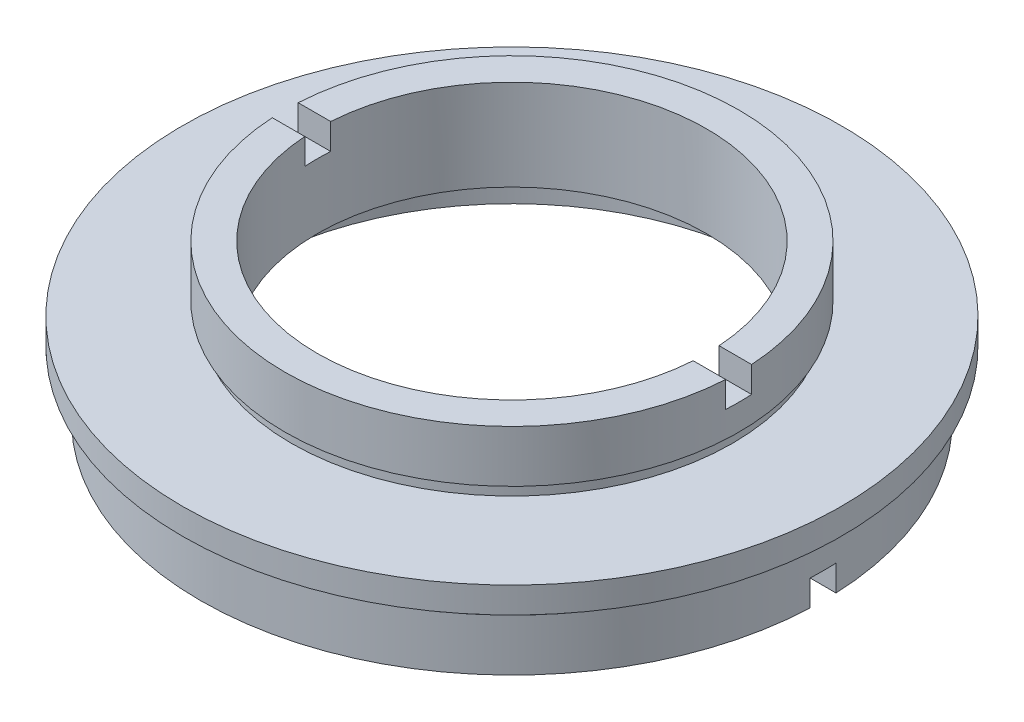
SolidWorks part; units mm, degrees
ref_plane "前视基准面" through (0, 0, 0) normal (0, 0, 1) x (1, 0, 0)
ref_plane "上视基准面" through (0, 0, 0) normal (0, 1, 0) x (1, 0, 0)
ref_plane "右视基准面" through (0, 0, 0) normal (1, 0, 0) x (0, 0, -1)
sketch "草图1" plane through (0, 0, 0) normal (0, 0, 1) x (1, 0, 0)
  line L0 (0, 22.6775) -> (0, 0) construction
  line L1 (-15, 12) -> (-17.5, 12)
  line L2 (-17.5, 12) -> (-17.5, 8)
  line L3 (-17.5, 8) -> (-17, 8)
  line L4 (-17, 8) -> (-17, 7)
  line L5 (-17, 7) -> (-25.4, 7)
  line L6 (-25.4, 7) -> (-25.4, 5)
  line L7 (-25.4, 5) -> (-23.5, 5)
  line L8 (-23.5, 5) -> (-23.5, 4)
  line L9 (-23.5, 4) -> (-24, 4)
  line L10 (-24, 4) -> (-24, 0)
  line L11 (-24, 0) -> (-20.5, 0)
  line L12 (-20.5, 0) -> (-20.5, 4)
  line L13 (-15, 5) -> (-21.1, 5)
  line L14 (-21.1, 5) -> (-21.1, 4)
  line L15 (-21.1, 4) -> (-20.5, 4)
  line L16 (-15, 12) -> (-15, 5)
  point P3 (-20.8, 4)
  point P5 (-25.4, 6)
  dimension "D2" = 1
  dimension "D3" = 1
  dimension "D4" = 5
  dimension "D5" = 5
  dimension "D6" = 17.5
  dimension "D7" = 25.4
  dimension "D8" = 24
  dimension "D9" = 23.5
  dimension "D10" = 17
  dimension "D11" = 20.5
  dimension "D12" = 0
  dimension "D13" = 21.1
  dimension "D14" = 15
  dimension "D15" = 12
  dimension "D16" = 7
  dimension "D17" = 1
revolve "旋转1" add sketch "草图1" angle 360 about L0
cosmetic thread "装饰螺纹线1"
cosmetic thread "装饰螺纹线2"
cosmetic thread "装饰螺纹线3"
cosmetic thread "装饰螺纹线4"
sketch "草图2" plane through (0, 0, 0) normal (1, 0, 0) x (0, 0, -1)
  line L0 (20.5, 12) -> (-20.5, 12) construction
  line L1 (-1, 13.594) -> (1, 13.594)
  line L2 (-1, 13.594) -> (-1, 10)
  line L3 (-1, 10) -> (1, 10)
  line L4 (1, 13.594) -> (1, 10)
  line L5 (-1, 2) -> (1, 2)
  line L6 (-1, 2) -> (-1, -4.6679)
  line L7 (-1, -4.6679) -> (1, -4.6679)
  line L8 (1, 2) -> (1, -4.6679)
  dimension "D1" = 2
  dimension "D2" = 1
  dimension "D3" = 2
  dimension "D4" = 1
  dimension "D5" = 2
  dimension "D6" = 2
extrude "切除-拉伸1" cut sketch "草图2" against normal mid plane 79
